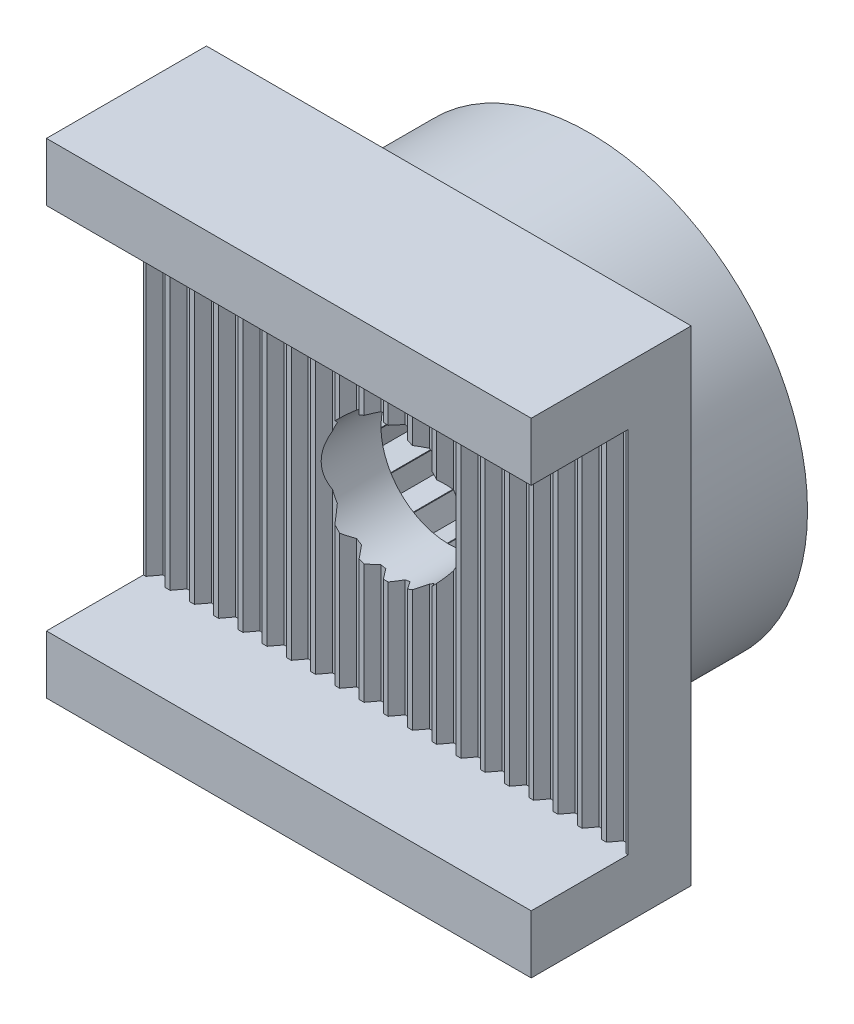
SolidWorks part; units mm, degrees
ref_plane "Face" through (0, 0, 0) normal (0, 0, 1) x (1, 0, 0)
ref_plane "Dessus" through (0, 0, 0) normal (0, 1, 0) x (1, 0, 0)
ref_plane "Droite" through (0, 0, 0) normal (1, 0, 0) x (0, 0, -1)
sketch "Esquisse1" plane through (0, 0, 0) normal (0, 0, 1) x (1, 0, 0)
  circle A0 centre (0, 0) radius 4.5
  line B0 (2.0116, -1.5509) -> (2.0116, -2.0116)
  line B1 (0.3258, 2.519) -> (0, 2.8448)
  line B2 (0.3373, 2.5175) -> (0.3258, 2.519)
  line B3 (0.7363, 2.7479) -> (0.3373, 2.5175)
  line B4 (0.9666, 2.3489) -> (0.7363, 2.7479)
  line B5 (0.9774, 2.3444) -> (0.9666, 2.3489)
  line B6 (1.4224, 2.4637) -> (0.9774, 2.3444)
  line B7 (1.5416, 2.0186) -> (1.4224, 2.4637)
  line B8 (1.5509, 2.0116) -> (1.5416, 2.0186)
  line B9 (2.0116, 2.0116) -> (1.5509, 2.0116)
  line B10 (2.0116, 1.5509) -> (2.0116, 2.0116)
  line B11 (2.0186, 1.5416) -> (2.0116, 1.5509)
  line B12 (2.4637, 1.4224) -> (2.0186, 1.5416)
  line B13 (2.3444, 0.9774) -> (2.4637, 1.4224)
  line B14 (2.3489, 0.9666) -> (2.3444, 0.9774)
  line B15 (2.7479, 0.7363) -> (2.3489, 0.9666)
  line B16 (2.5175, 0.3373) -> (2.7479, 0.7363)
  line B17 (2.519, 0.3258) -> (2.5175, 0.3373)
  line B18 (2.8448, 0) -> (2.519, 0.3258)
  line B19 (2.519, -0.3258) -> (2.8448, 0)
  line B20 (2.5175, -0.3373) -> (2.519, -0.3258)
  line B21 (2.7479, -0.7363) -> (2.5175, -0.3373)
  line B22 (2.3489, -0.9666) -> (2.7479, -0.7363)
  line B23 (2.3444, -0.9774) -> (2.3489, -0.9666)
  line B24 (2.4637, -1.4224) -> (2.3444, -0.9774)
  line B25 (2.0186, -1.5416) -> (2.4637, -1.4224)
  line B26 (2.0116, -1.5509) -> (2.0186, -1.5416)
  line B27 (1.5509, -2.0116) -> (2.0116, -2.0116)
  line B28 (1.5416, -2.0186) -> (1.5509, -2.0116)
  line B29 (1.4224, -2.4637) -> (1.5416, -2.0186)
  line B30 (0.9774, -2.3444) -> (1.4224, -2.4637)
  line B31 (0.9666, -2.3489) -> (0.9774, -2.3444)
  line B32 (0.7363, -2.7479) -> (0.9666, -2.3489)
  line B33 (0.3373, -2.5175) -> (0.7363, -2.7479)
  line B34 (0.3258, -2.519) -> (0.3373, -2.5175)
  line B35 (0, -2.8448) -> (0.3258, -2.519)
  line B36 (-0.3258, -2.519) -> (0, -2.8448)
  line B37 (-0.3373, -2.5175) -> (-0.3258, -2.519)
  line B38 (-0.7363, -2.7479) -> (-0.3373, -2.5175)
  line B39 (-0.9666, -2.3489) -> (-0.7363, -2.7479)
  line B40 (-0.9774, -2.3444) -> (-0.9666, -2.3489)
  line B41 (-1.4224, -2.4637) -> (-0.9774, -2.3444)
  line B42 (-1.5416, -2.0186) -> (-1.4224, -2.4637)
  line B43 (-1.5509, -2.0116) -> (-1.5416, -2.0186)
  line B44 (-2.0116, -2.0116) -> (-1.5509, -2.0116)
  line B45 (-2.0116, -1.5509) -> (-2.0116, -2.0116)
  line B46 (-2.0186, -1.5416) -> (-2.0116, -1.5509)
  line B47 (-2.4637, -1.4224) -> (-2.0186, -1.5416)
  line B48 (-2.3444, -0.9774) -> (-2.4637, -1.4224)
  line B49 (-2.3489, -0.9666) -> (-2.3444, -0.9774)
  line B50 (-2.7479, -0.7363) -> (-2.3489, -0.9666)
  line B51 (-2.5175, -0.3373) -> (-2.7479, -0.7363)
  line B52 (-2.519, -0.3258) -> (-2.5175, -0.3373)
  line B53 (-2.8448, 0) -> (-2.519, -0.3258)
  line B54 (-2.519, 0.3258) -> (-2.8448, 0)
  line B55 (-2.5175, 0.3373) -> (-2.519, 0.3258)
  line B56 (-2.7479, 0.7363) -> (-2.5175, 0.3373)
  line B57 (-2.3489, 0.9666) -> (-2.7479, 0.7363)
  line B58 (-2.3444, 0.9774) -> (-2.3489, 0.9666)
  line B59 (-2.4637, 1.4224) -> (-2.3444, 0.9774)
  line B60 (-2.0186, 1.5416) -> (-2.4637, 1.4224)
  line B61 (-2.0116, 1.5509) -> (-2.0186, 1.5416)
  line B62 (-2.0116, 2.0116) -> (-2.0116, 1.5509)
  line B63 (-1.5509, 2.0116) -> (-2.0116, 2.0116)
  line B64 (-1.5416, 2.0186) -> (-1.5509, 2.0116)
  line B65 (-1.4224, 2.4637) -> (-1.5416, 2.0186)
  line B66 (-0.9774, 2.3444) -> (-1.4224, 2.4637)
  line B67 (-0.9666, 2.3489) -> (-0.9774, 2.3444)
  line B68 (-0.7363, 2.7479) -> (-0.9666, 2.3489)
  line B69 (-0.3373, 2.5175) -> (-0.7363, 2.7479)
  line B70 (-0.3258, 2.519) -> (-0.3373, 2.5175)
  line B71 (0, 2.8448) -> (-0.3258, 2.519)
  dimension "D1" = 9
sketch_block_instance "Block1-1"
sketch_block "Block1"
extrude "Boss.-Extru.1" add sketch "Esquisse1" along normal blind 2.9
sketch "Esquisse2" plane through (0, 0, 2.9) normal (0, 0, 1) x (1, 0, 0)
  line L1 (-5, 5) -> (5, 5)
  line L2 (-5, 5) -> (-5, -5)
  line L3 (-5, -5) -> (5, -5)
  line L4 (5, 5) -> (5, -5)
  line L5 (-5, 5) -> (5, -5) construction
  line L6 (-5, -5) -> (5, 5) construction
  circle A0 centre (0, 0) radius 1.4
  point P0 (0, 0)
  dimension "D3" = 2.8
  dimension "D1" = 10
  dimension "D2" = 10
extrude "Boss.-Extru.2" add sketch "Esquisse2" along normal blind 1.3
sketch "Esquisse3" plane through (0, 0, 4.2) normal (0, 0, 1) x (1, 0, 0)
  line L0 (5, -5) -> (5, 5) construction
  line L1 (-5, 5) -> (5, 5)
  line L2 (-5, 5) -> (-5, 3.8)
  line L3 (-5, 3.8) -> (5, 3.8)
  line L4 (5, 5) -> (5, 3.8)
  line L6 (-5, -5) -> (5, -5)
  line L7 (-5, -5) -> (-5, -3.8)
  line L8 (-5, -3.8) -> (5, -3.8)
  line L9 (5, -5) -> (5, -3.8)
  dimension "D1" = 1.2
  dimension "D2" = 1.2
extrude "Boss.-Extru.3" add sketch "Esquisse3" along direction (0, 0, 1) on the side of the normal offset from surface (2 mm away) 3.3
sketch "Esquisse4" plane through (0, 3.8, 0) normal (0, -1, 0) x (1, 0, 0)
  line L0 (-4.55, 4.2) -> (-4.7, 4)
  line L1 (-4.8, 4) -> (-4.95, 4.2)
  line L2 (-4.95, 4.2) -> (-4.55, 4.2)
  line L3 (-4.75, 4.2) -> (-4.75, 4) construction
  line L4 (-4.8, 4) -> (-4.7, 4)
  line L5 (-5, 4.2) -> (5, 4.2) construction
  point P5 (-4.75, 3.9789)
  point P6 (0, 0)
  point P10 (-4.9582, 4.2)
  dimension "D1" = 0.4
  dimension "D2" = 0.2
  dimension "D3" = 0.1
  dimension "D4" = 0.05
extrude "Enlèv. mat.-Extru.1" cut sketch "Esquisse4" along normal up to surface (7.6 mm away) up to face at (0, -3.8, 5.2)
pattern_linear "Répétition linéaire4" count 20 spacing 0.5 along (1, 0, 0) of "Enlèv. mat.-Extru.1"
